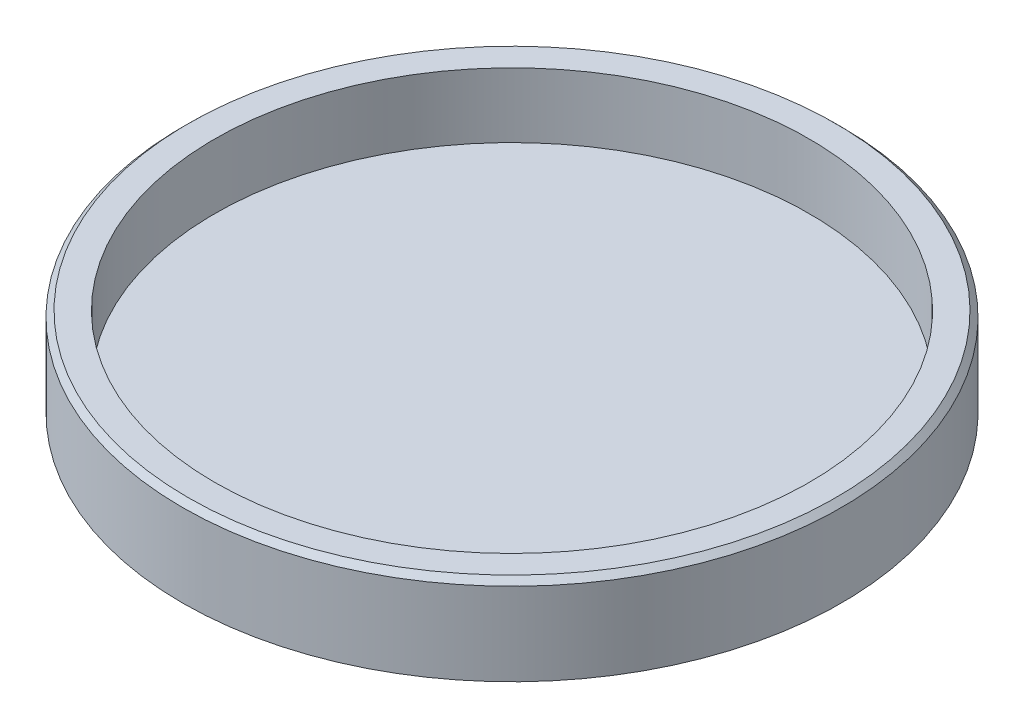
SolidWorks part; units mm, degrees
ref_plane "Front Plane" through (0, 0, 0) normal (0, 0, 1) x (1, 0, 0)
ref_plane "Top Plane" through (0, 0, 0) normal (0, 1, 0) x (1, 0, 0)
ref_plane "Right Plane" through (0, 0, 0) normal (1, 0, 0) x (0, 0, -1)
sketch "Sketch1" plane through (0, 0, 0) normal (0, 0, 1) x (1, 0, 0)
  line L0 (0, 9.5559) -> (0, -9.5559) construction
  line L1 (0, -1.905) -> (18.5, -1.905)
  line L2 (18.5, -1.905) -> (18.5, 2.1217)
  line L3 (20.5, 1.7682) -> (20.5, -3.3783)
  line L4 (20.5, -3.3783) -> (0, -3.3783)
  line L5 (18.5, 2.1217) -> (20.1464, 2.1217)
  line L6 (20.1464, 2.1217) -> (20.5, 1.7682)
  line L7 (0, -1.905) -> (0, -3.3783)
  point P4 (0, 0)
  dimension "D1" = 5.5
  dimension "D2" = 20.5
  dimension "D3" = 18.5
  dimension "D4" = 0.5
  dimension "D5" = 45
  dimension "D6" = 45
revolve "Revolve1" add sketch "Sketch1" angle 360 about L0
